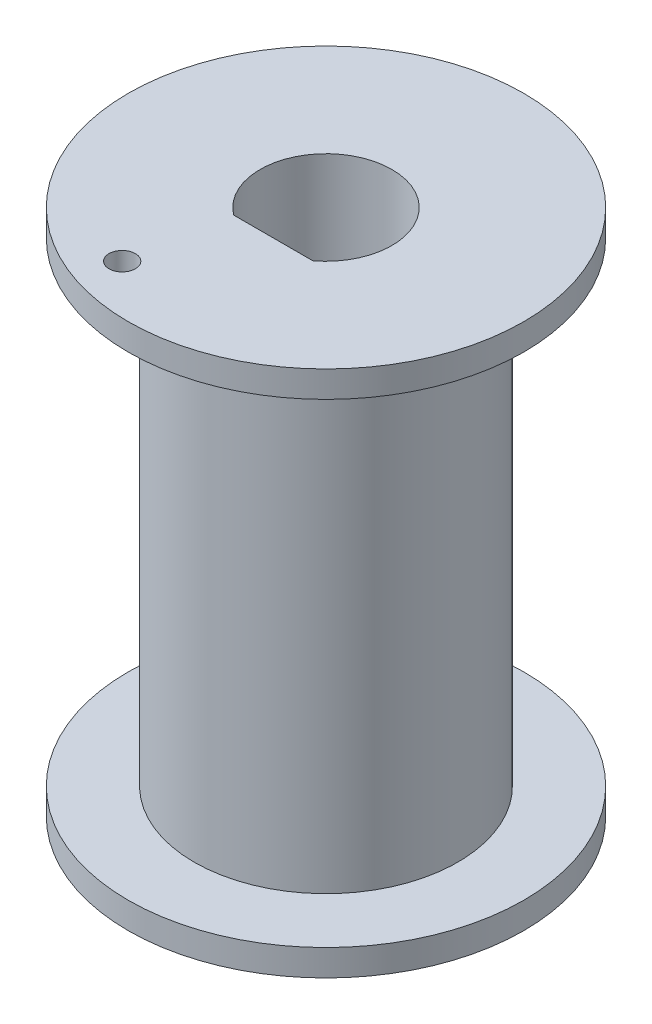
SolidWorks part; units mm, degrees
ref_plane "Front Plane" through (0, 0, 0) normal (0, 0, 1) x (1, 0, 0)
ref_plane "Top Plane" through (0, 0, 0) normal (0, 1, 0) x (1, 0, 0)
ref_plane "Right Plane" through (0, 0, 0) normal (1, 0, 0) x (0, 0, -1)
sketch "Sketch1" plane through (0, 0, 0) normal (0, 1, 0) x (1, 0, 0)
  circle A0 centre (0, 0) radius 5
extrude "Boss-Extrude1" add sketch "Sketch1" along normal blind 20
sketch "Sketch2" plane through (0, 20, 0) normal (0, 1, 0) x (1, 0, 0)
  circle A0 centre (0, 0) radius 2.5
extrude "Cut-Extrude1" cut sketch "Sketch2" against normal through all
sketch "Sketch3" plane through (0, 20, 0) normal (0, 1, 0) x (1, 0, 0)
  line L2 (1.5, -2) -> (-1.5, -2)
  arc A0 (-1.5, -2) -> (1.5, -2) centre (0, 0) ccw
extrude "Boss-Extrude2" add sketch "Sketch3" against normal blind 18
sketch "Sketch4" plane through (0, 20, 0) normal (0, 1, 0) x (1, 0, 0)
  line L0 (1.5, -2) -> (-1.5, -2)
  circle A0 centre (0, 0) radius 7.5
  arc A1 (1.5, -2) -> (-1.5, -2) centre (0, 0) ccw
sketch "Sketch5" plane through (0, 0, 0) normal (0, -1, 0) x (1, 0, 0)
  circle A0 centre (0, 0) radius 7.5
  circle A1 centre (0, 0) radius 2.5
extrude "Boss-Extrude3" add sketch "Sketch5" against normal blind 1
extrude "Boss-Extrude4" add sketch "Sketch4" against normal blind 1
sketch "Sketch7" plane through (0, 19, 0) normal (0, -1, 0) x (1, 0, 0)
  circle A0 centre (-2.1009, 5.6282) radius 0.5
extrude "Cut-Extrude2" cut sketch "Sketch7" against normal through all
